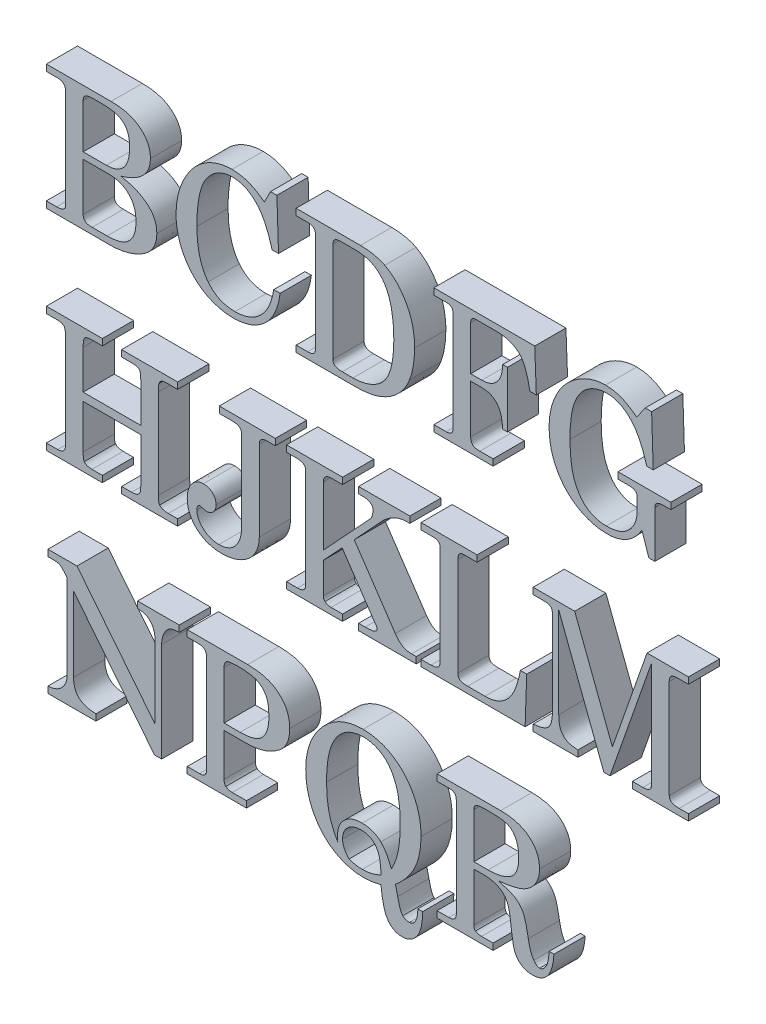
SolidWorks part; units mm, degrees
ref_plane "Plan de face" through (0, 0, 0) normal (0, 0, 1) x (1, 0, 0)
ref_plane "Plan de dessus" through (0, 0, 0) normal (0, 1, 0) x (1, 0, 0)
ref_plane "Plan de droite" through (0, 0, 0) normal (1, 0, 0) x (0, 0, -1)
sketch "Esquisse1" plane through (0, 0, 0) normal (0, 0, 1) x (1, 0, 0)
  text T0 "BCDFG\r\nHJKLM\r\nNPQR\r\n" font "Century Schoolbook" height 40
extrude "Boss.-Extru.1" add sketch "Esquisse1" along normal blind 10
